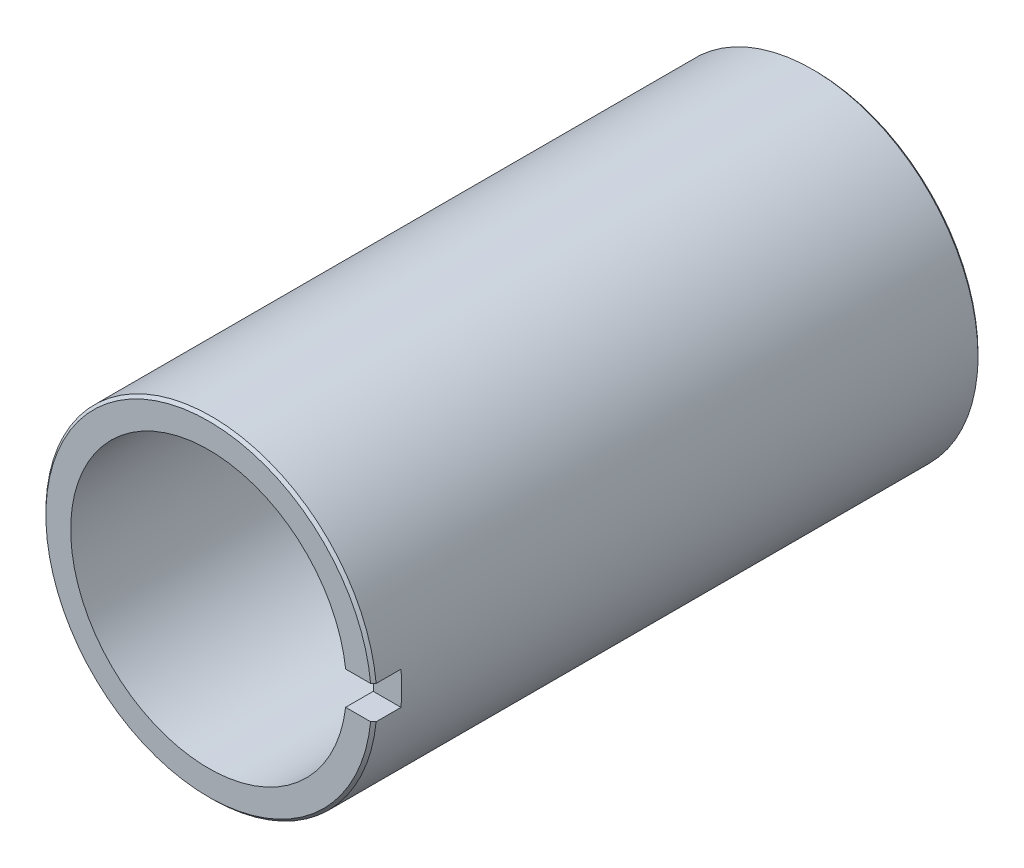
SolidWorks part; units mm, degrees
ref_plane "Front Plane" through (0, 0, 0) normal (0, 0, 1) x (1, 0, 0)
ref_plane "Top Plane" through (0, 0, 0) normal (0, 1, 0) x (1, 0, 0)
ref_plane "Right Plane" through (0, 0, 0) normal (1, 0, 0) x (0, 0, -1)
sketch "Sketch1" plane through (0, 0, 0) normal (0, 0, 1) x (1, 0, 0)
  circle A0 centre (0, 0) radius 30
  circle A1 centre (0, 0) radius 25
  dimension "D1" = 60
  dimension "D2" = 50
extrude "Boss-Extrude1" add sketch "Sketch1" along normal blind 109.9
sketch "Sketch2" plane through (0, 0, 0) normal (1, 0, 0) x (0, 0, -1)
  line L0 (-109.9, 30) -> (-109.9, -30) construction
  line L1 (-109.9, 3) -> (-104.9, 3)
  line L2 (-109.9, 3) -> (-109.9, -3)
  line L3 (-109.9, -3) -> (-104.9, -3)
  line L4 (-104.9, 3) -> (-104.9, -3)
  dimension "D1" = 5
  dimension "D2" = 6
  dimension "D3" = 3
extrude "Cut-Extrude1" cut sketch "Sketch2" along normal through all
chamfer "Chamfer1" distance 0.5 2 edges at (-30, 0, 109.9) (30, 0, 0)
